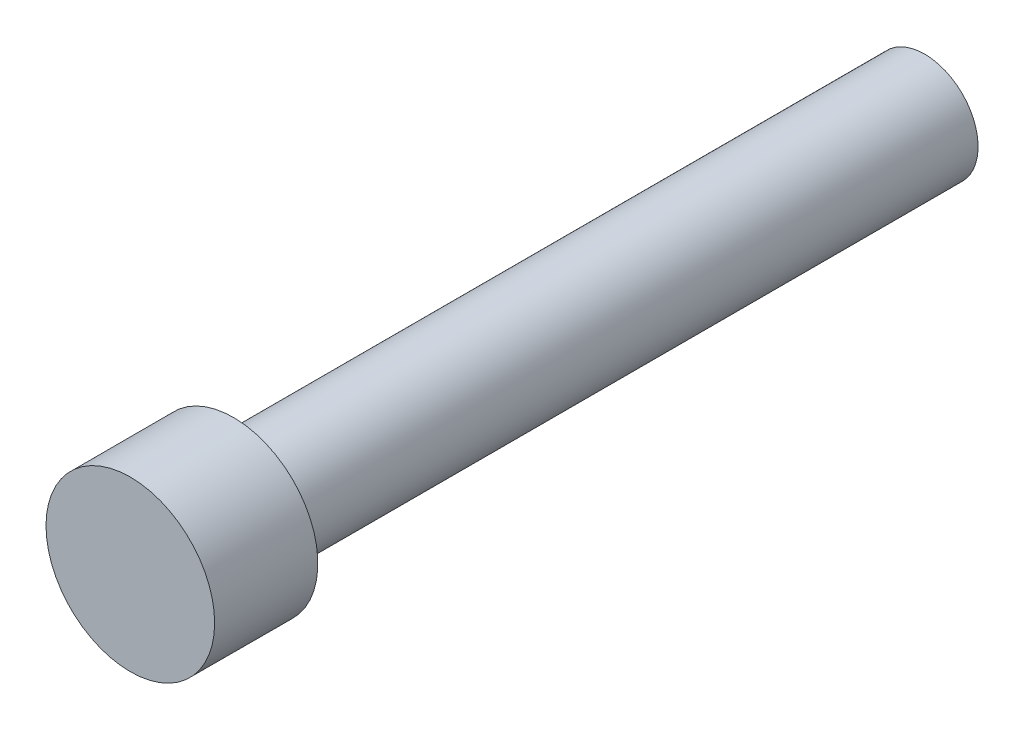
SolidWorks part; units mm, degrees
ref_plane "Front Plane" through (0, 0, 0) normal (0, 0, 1) x (1, 0, 0)
ref_plane "Top Plane" through (0, 0, 0) normal (0, 1, 0) x (1, 0, 0)
ref_plane "Right Plane" through (0, 0, 0) normal (1, 0, 0) x (0, 0, -1)
sketch "Sketch1" plane through (0, 0, 0) normal (0, 0, 1) x (1, 0, 0)
  circle A0 centre (0, 0) radius 2.3241
extrude "Extrude1" add sketch "Sketch1" along normal blind 21.8948
sketch "Sketch3" plane through (0, 0, 0) normal (0, 0, -1) x (-1, 0, 0)
  circle A0 centre (0, 0) radius 1.4732
extrude "Extrude2" cut sketch "Sketch3" against normal blind 19.05 flip side to cut
